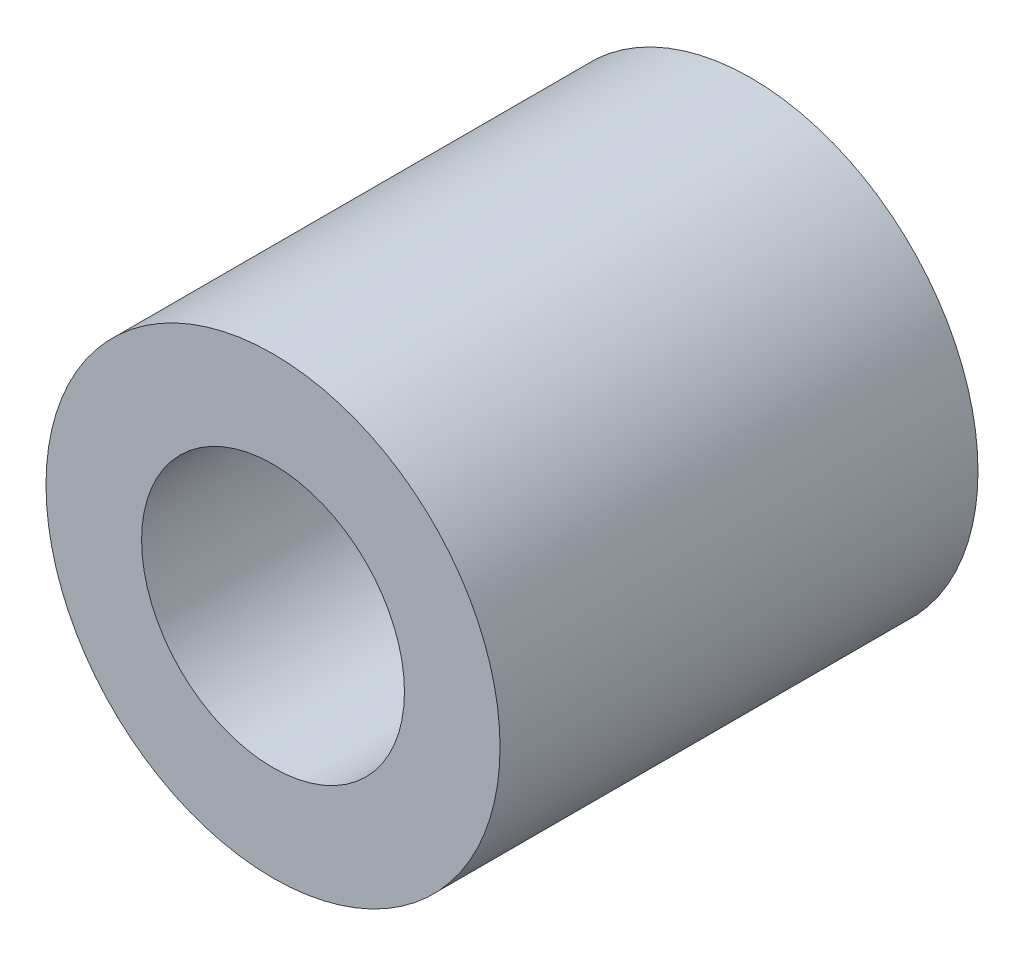
SolidWorks part; units mm, degrees
ref_plane "Alzado" through (0, 0, 0) normal (0, 0, 1) x (1, 0, 0)
ref_plane "Planta" through (0, 0, 0) normal (0, 1, 0) x (1, 0, 0)
ref_plane "Vista lateral" through (0, 0, 0) normal (1, 0, 0) x (0, 0, -1)
sketch "Croquis1" plane through (0, 0, 0) normal (0, 0, 1) x (1, 0, 0)
  circle A0 centre (0, 0) radius 4.75
  circle A1 centre (0, 0) radius 2.75
  dimension "D1" = 9.5
  dimension "D2" = 5.5
extrude "Saliente-Extruir1" add sketch "Croquis1" along normal blind 10
